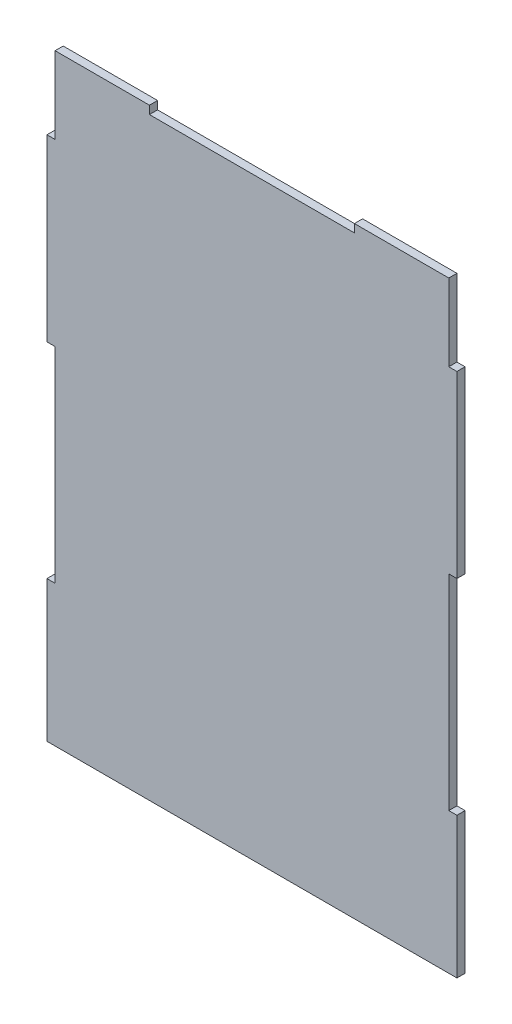
SolidWorks part; units mm, degrees
ref_plane "Front Plane" through (0, 0, 0) normal (0, 0, 1) x (1, 0, 0)
ref_plane "Top Plane" through (0, 0, 0) normal (0, 1, 0) x (1, 0, 0)
ref_plane "Right Plane" through (0, 0, 0) normal (1, 0, 0) x (0, 0, -1)
sketch "Sketch1" plane through (0, 0, 0) normal (0, 0, 1) x (1, 0, 0)
  line L0 (-346.1651, 0) -> (340.816, 0) construction
  line L1 (0, 224.6635) -> (0, -225.4276) construction
  line L2 (0, 0) -> (80, 0)
  line L3 (80, 0) -> (80, 55)
  line L4 (80, 55) -> (76.825, 55)
  line L5 (76.825, 55) -> (76.825, 135)
  line L6 (76.825, 135) -> (80, 135)
  line L7 (80, 135) -> (80, 205)
  line L8 (80, 205) -> (76.825, 205)
  line L9 (76.825, 205) -> (76.825, 235)
  line L10 (76.825, 235) -> (40, 235)
  line L11 (40, 235) -> (40, 231.825)
  line L12 (40, 231.825) -> (0, 231.825)
  line L13 (-40, 235) -> (-40, 231.825)
  line L14 (-76.825, 235) -> (-40, 235)
  line L15 (-76.825, 205) -> (-76.825, 235)
  line L16 (-80, 205) -> (-76.825, 205)
  line L17 (-80, 135) -> (-80, 205)
  line L18 (-76.825, 135) -> (-80, 135)
  line L19 (-76.825, 55) -> (-76.825, 135)
  line L20 (-80, 55) -> (-76.825, 55)
  line L21 (-80, 0) -> (-80, 55)
  line L22 (-40, 231.825) -> (0, 231.825)
  line L23 (-80, 0) -> (0, 0)
  dimension "D1" = 80
  dimension "D2" = 55
  dimension "D3" = 3.175
  dimension "D4" = 80
  dimension "D5" = 3.175
  dimension "D6" = 70
  dimension "D7" = 3.175
  dimension "D8" = 30
  dimension "D9" = 36.825
  dimension "D10" = 3.175
  dimension "D11" = 40
extrude "Boss-Extrude1" add sketch "Sketch1" against normal blind 3.175
